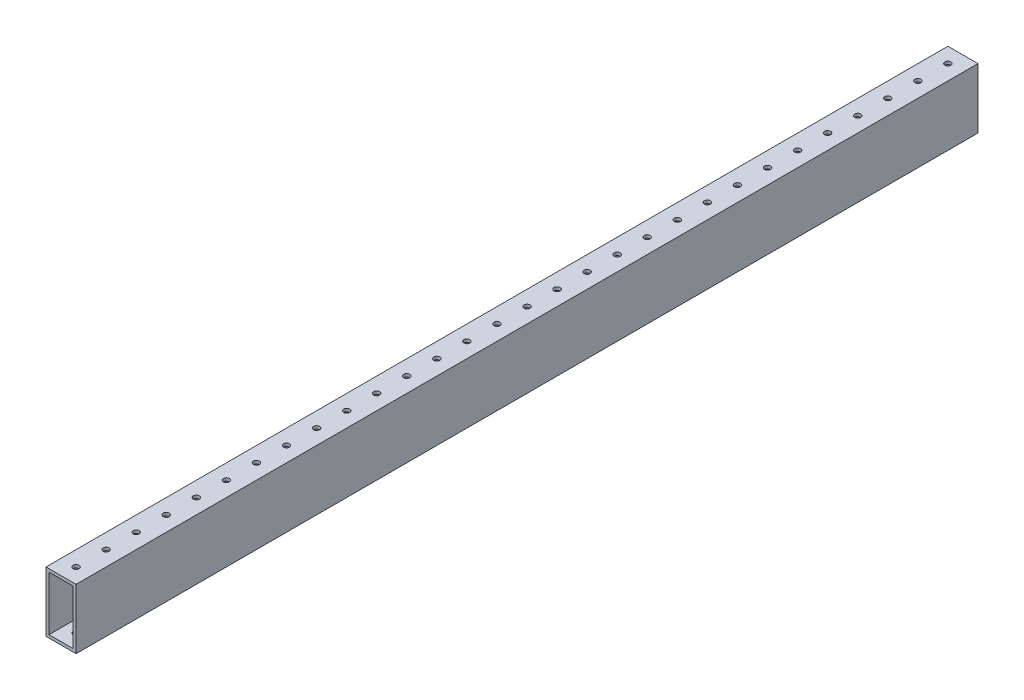
SolidWorks part; units mm, degrees
ref_plane "Front Plane" through (0, 0, 0) normal (0, 0, 1) x (1, 0, 0)
ref_plane "Top Plane" through (0, 0, 0) normal (0, 1, 0) x (1, 0, 0)
ref_plane "Right Plane" through (0, 0, 0) normal (1, 0, 0) x (0, 0, -1)
sketch "Sketch2" plane through (0, 0, 0) normal (0, 1, 0) x (1, 0, 0)
  line L1 (0, 0) -> (25.4, 0)
  line L2 (0, 0) -> (0, 762)
  line L3 (0, 762) -> (25.4, 762)
  line L4 (25.4, 0) -> (25.4, 762)
  circle A0 centre (12.7, 12.7) radius 2.54
  circle A1 centre (12.7, 38.1) radius 2.54
  circle A2 centre (12.7, 63.5) radius 2.54
  circle A3 centre (12.7, 88.9) radius 2.54
  circle A4 centre (12.7, 114.3) radius 2.54
  circle A5 centre (12.7, 139.7) radius 2.54
  circle A6 centre (12.7, 165.1) radius 2.54
  circle A7 centre (12.7, 190.5) radius 2.54
  circle A8 centre (12.7, 215.9) radius 2.54
  circle A9 centre (12.7, 241.3) radius 2.54
  circle A10 centre (12.7, 266.7) radius 2.54
  circle A11 centre (12.7, 292.1) radius 2.54
  circle A12 centre (12.7, 317.5) radius 2.54
  circle A13 centre (12.7, 342.9) radius 2.54
  circle A14 centre (12.7, 368.3) radius 2.54
  circle A15 centre (12.7, 393.7) radius 2.54
  circle A16 centre (12.7, 419.1) radius 2.54
  circle A17 centre (12.7, 444.5) radius 2.54
  circle A18 centre (12.7, 469.9) radius 2.54
  circle A19 centre (12.7, 495.3) radius 2.54
  circle A20 centre (12.7, 520.7) radius 2.54
  circle A21 centre (12.7, 546.1) radius 2.54
  circle A22 centre (12.7, 571.5) radius 2.54
  circle A23 centre (12.7, 596.9) radius 2.54
  circle A24 centre (12.7, 622.3) radius 2.54
  circle A25 centre (12.7, 647.7) radius 2.54
  circle A26 centre (12.7, 673.1) radius 2.54
  circle A27 centre (12.7, 698.5) radius 2.54
  circle A28 centre (12.7, 723.9) radius 2.54
  circle A29 centre (12.7, 749.3) radius 2.54
  dimension "D3" = 5.08
  dimension "D1" = 762
  dimension "D2" = 25.4
  dimension "D4" = 12.7
  dimension "D5" = 12.7
  dimension "D6" = 30
extrude "Boss-Extrude1" add sketch "Sketch2" along normal blind 50.8
sketch "Sketch3" plane through (0, 0, 0) normal (0, 0, 1) x (1, 0, 0)
  line L1 (0, 0) -> (25.4, 0)
  line L2 (0, 0) -> (0, 50.8)
  line L3 (0, 50.8) -> (25.4, 50.8)
  line L4 (25.4, 0) -> (25.4, 50.8)
  line L16 (2.54, 2.54) -> (22.86, 2.54)
  line L17 (22.86, 2.54) -> (22.86, 48.26)
  line L18 (22.86, 48.26) -> (2.54, 48.26)
  line L19 (2.54, 48.26) -> (2.54, 2.54)
  line L20 (2.54, 2.54) -> (22.86, 2.54)
  line L21 (22.86, 2.54) -> (22.86, 48.26)
  line L22 (22.86, 48.26) -> (2.54, 48.26)
  line L23 (2.54, 48.26) -> (2.54, 2.54)
  dimension "D1" = 2.54
extrude "Cut-Extrude1" cut sketch "Sketch3" against normal through all flip side to cut
